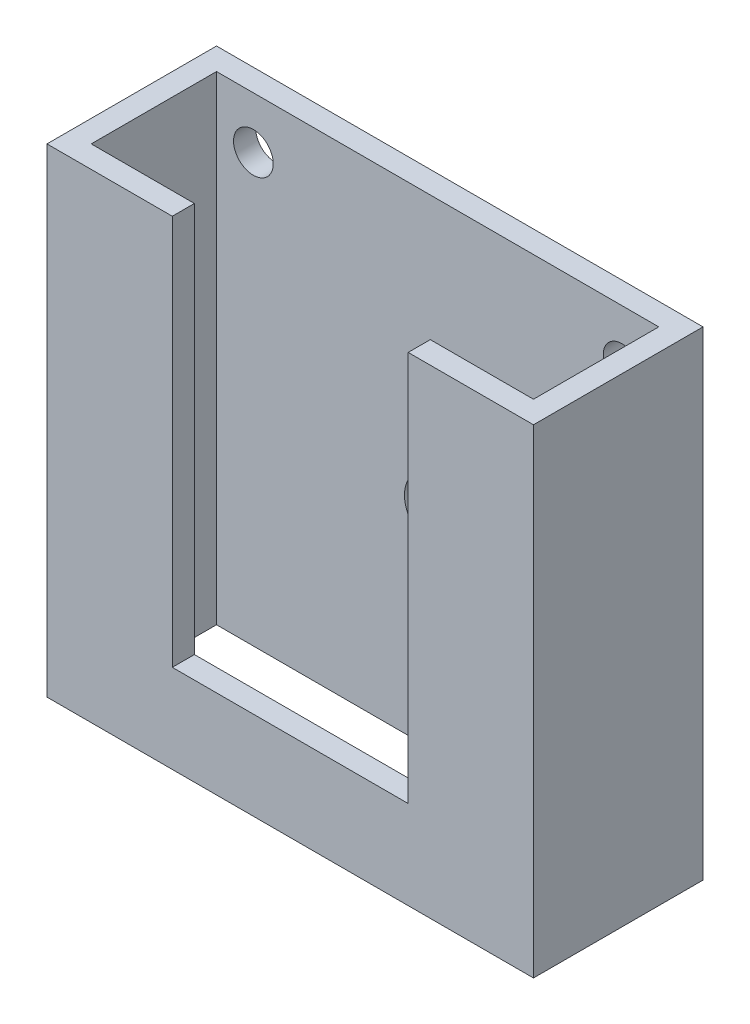
SolidWorks part; units mm, degrees
ref_plane "Front Plane" through (0, 0, 0) normal (0, 0, 1) x (1, 0, 0)
ref_plane "Top Plane" through (0, 0, 0) normal (0, 1, 0) x (1, 0, 0)
ref_plane "Right Plane" through (0, 0, 0) normal (1, 0, 0) x (0, 0, -1)
sketch "Sketch1" plane through (0, 0, 0) normal (1, 0, 0) x (0, 0, -1)
  line L0 (0, 0) -> (0, -65)
  line L1 (0, -65) -> (-23, -65)
  line L2 (-23, -65) -> (-23, 0)
  line L3 (-23, 0) -> (0, 0)
  dimension "D1" = 65
  dimension "D2" = 23
extrude "Boss-Extrude1" add sketch "Sketch1" against normal blind 66
sketch "Sketch2" plane through (0, 0, 0) normal (0, 1, 0) x (1, 0, 0)
  line L0 (-33, 0) -> (-33, -23) construction
  line L1 (-66, 0) -> (0, 0) construction
  line L2 (-66, -23) -> (0, -23) construction
  line L3 (-66, -11.5) -> (0, -11.5) construction
  line L4 (-66, 0) -> (-66, -23) construction
  line L5 (0, 0) -> (0, -23) construction
  line L7 (-63, -20) -> (-3, -20)
  line L8 (-63, -20) -> (-63, -3)
  line L9 (-63, -3) -> (-3, -3)
  line L10 (-3, -20) -> (-3, -3)
  line L11 (-63, -20) -> (-3, -3) construction
  line L12 (-63, -3) -> (-3, -20) construction
  point P12 (-33, -11.5)
  point P17 (-3, -11.5)
  point P18 (-63, -11.5)
  dimension "D1" = 3
  dimension "D2" = 3
  dimension "D3" = 3
  dimension "D4" = 3
extrude "Cut-Extrude1" cut sketch "Sketch2" against normal through all
sketch "Sketch3" plane through (0, 0, 23) normal (0, 0, 1) x (1, 0, 0)
  line L0 (-66, 0) -> (0, 0) construction
  line L1 (-49, 0) -> (-17, 0)
  line L2 (-49, 0) -> (-49, -53)
  line L3 (-49, -53) -> (-17, -53)
  line L4 (-17, 0) -> (-17, -53)
  line L5 (-66, 0) -> (-66, -65) construction
  line L6 (0, 0) -> (0, -65) construction
  line L7 (-66, -65) -> (0, -65) construction
  dimension "D1" = 17
  dimension "D2" = 17
  dimension "D3" = 32
  dimension "D4" = 12
  dimension "D5" = 53
extrude "Cut-Extrude2" cut sketch "Sketch3" against normal up to next
sketch "Sketch5" plane through (0, 0, 0) normal (0, 0, -1) x (-1, 0, 0)
  line L0 (33, -65) -> (33, 0) construction
  line L1 (66, -65) -> (0, -65) construction
  line L2 (66, 0) -> (0, 0) construction
  line L3 (0, -32.5) -> (66, -32.5) construction
  line L4 (0, -65) -> (0, 0) construction
  line L5 (66, -65) -> (66, 0) construction
  circle A0 centre (33, -37) radius 4.5
  circle A1 centre (8, -7) radius 2.5306
  circle A2 centre (58, -7) radius 2.6928
  dimension "D2" = 9
  dimension "D1" = 28
  dimension "D3" = 8
  dimension "D4" = 8
  dimension "D5" = 7
  dimension "D6" = 7
extrude "Cut-Extrude3" cut sketch "Sketch5" against normal up to next
